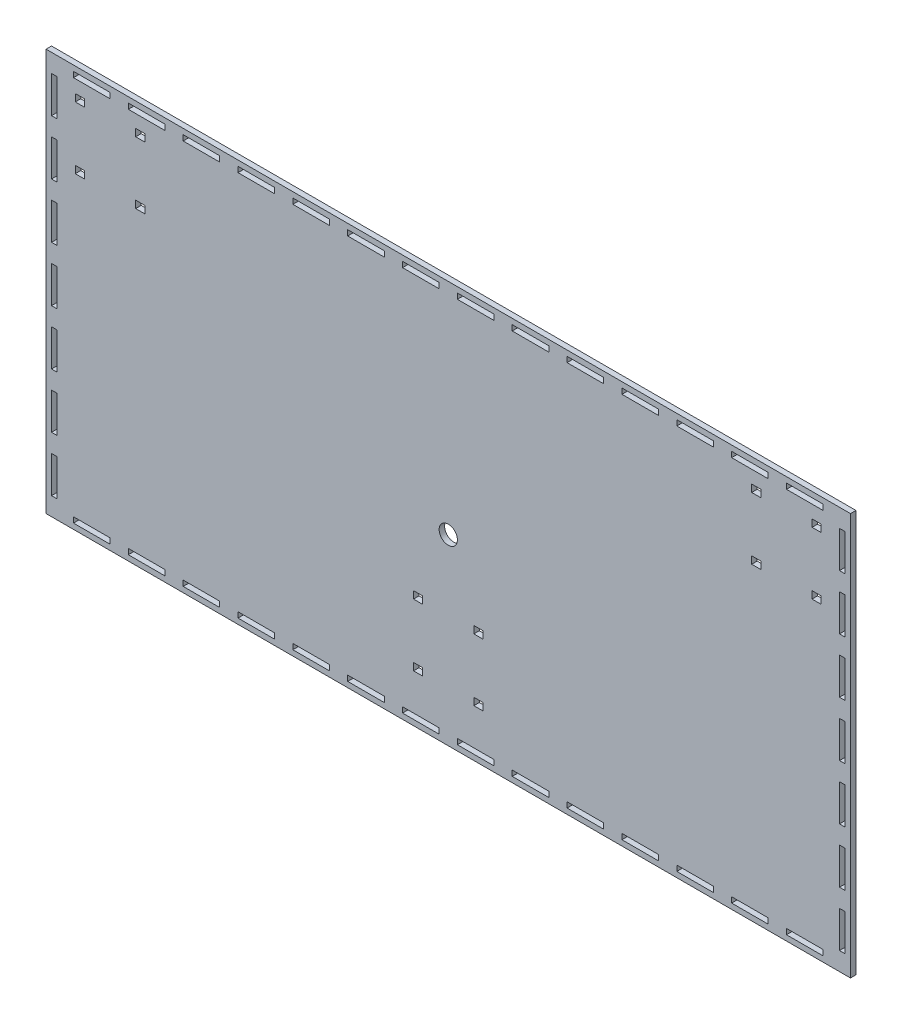
SolidWorks part; units mm, degrees
ref_plane "Plan de face" through (0, 0, 0) normal (0, 0, 1) x (1, 0, 0)
ref_plane "Plan de dessus" through (0, 0, 0) normal (0, 1, 0) x (1, 0, 0)
ref_plane "Plan de droite" through (0, 0, 0) normal (1, 0, 0) x (0, 0, -1)
sketch "Esquisse1" plane through (0, 0, 0) normal (0, 0, 1) x (1, 0, 0)
  line L1 (-220, 110) -> (220, 110)
  line L2 (-220, 110) -> (-220, -110)
  line L3 (-220, -110) -> (220, -110)
  line L4 (220, 110) -> (220, -110)
  line L5 (-220, 110) -> (220, -110) construction
  line L6 (-220, -110) -> (220, 110) construction
  point P0 (0, 0)
  dimension "D1" = 440
  dimension "D2" = 220
extrude "Boss.-Extru.1" add sketch "Esquisse1" along normal blind 3
sketch "Esquisse2" plane through (0, 0, 3) normal (0, 0, 1) x (1, 0, 0)
  line L0 (-220, -10) -> (220, -10) construction
  line L1 (-220, 110) -> (-220, -110) construction
  line L2 (220, -110) -> (220, 110) construction
  line L3 (0, 110) -> (0, -110) construction
  line L4 (220, 110) -> (-220, 110) construction
  line L5 (-220, -110) -> (220, -110) construction
  circle A0 centre (0, -10) radius 5
  dimension "D2" = 10
  dimension "D1" = 100
extrude "Enlèv. mat.-Extru.1" cut sketch "Esquisse2" against normal blind 3
sketch "Esquisse3" plane through (0, 0, 3) normal (0, 0, 1) x (1, 0, 0)
  line L0 (-185, 94) -> (-185, 62) construction
  line L1 (-201, 78) -> (-169, 78) construction
  line L2 (-220, 110) -> (-220, -110) construction
  line L3 (220, 110) -> (-220, 110) construction
  line L4 (-171, 95) -> (-199, 95) construction
  line L5 (-204, 97) -> (-199, 97)
  line L6 (-204, 97) -> (-204, 93)
  line L7 (-204, 93) -> (-199, 93)
  line L8 (-199, 97) -> (-199, 93)
  line L9 (-204, 97) -> (-199, 93) construction
  line L10 (-204, 93) -> (-199, 97) construction
  line L11 (-166, 97) -> (-171, 97)
  line L12 (-166, 97) -> (-166, 93)
  line L13 (-166, 93) -> (-171, 93)
  line L14 (-171, 97) -> (-171, 93)
  line L15 (-166, 97) -> (-171, 93) construction
  line L16 (-166, 93) -> (-171, 97) construction
  line L17 (-166, 63) -> (-171, 63)
  line L18 (-166, 59) -> (-166, 63)
  line L19 (-166, 59) -> (-171, 59)
  line L20 (-171, 59) -> (-171, 63)
  line L21 (-199, 59) -> (-199, 63)
  line L22 (-204, 63) -> (-199, 63)
  line L23 (-204, 59) -> (-204, 63)
  line L24 (-204, 59) -> (-199, 59)
  line L25 (0, 110) -> (0, -110) construction
  line L26 (-220, -110) -> (220, -110) construction
  line L27 (-220, 0) -> (220, 0) construction
  line L28 (220, -110) -> (220, 110) construction
  line L29 (171, 59) -> (171, 63)
  line L30 (166, 59) -> (171, 59)
  line L31 (166, 59) -> (166, 63)
  line L32 (166, 63) -> (171, 63)
  line L33 (204, 59) -> (199, 59)
  line L34 (204, 59) -> (204, 63)
  line L35 (204, 63) -> (199, 63)
  line L36 (199, 59) -> (199, 63)
  line L37 (166, 93) -> (171, 93)
  line L38 (166, 97) -> (166, 93)
  line L39 (166, 97) -> (171, 97)
  line L40 (171, 97) -> (171, 93)
  line L41 (199, 97) -> (199, 93)
  line L42 (204, 93) -> (199, 93)
  line L43 (204, 97) -> (204, 93)
  line L44 (204, 97) -> (199, 97)
  line L53 (-19, -50) -> (-14, -50)
  line L54 (-19, -46) -> (-19, -50)
  line L55 (-19, -46) -> (-14, -46)
  line L56 (-14, -46) -> (-14, -50)
  line L57 (14, -46) -> (14, -50)
  line L58 (19, -46) -> (14, -46)
  line L59 (19, -46) -> (19, -50)
  line L60 (19, -50) -> (14, -50)
  line L61 (-28.5071, -65) -> (30.7799, -65) construction
  line L63 (19, -84) -> (14, -84)
  line L64 (19, -84) -> (19, -80)
  line L65 (19, -80) -> (14, -80)
  line L66 (14, -84) -> (14, -80)
  line L67 (-14, -84) -> (-14, -80)
  line L68 (-19, -84) -> (-14, -84)
  line L69 (-19, -84) -> (-19, -80)
  line L70 (-19, -80) -> (-14, -80)
  circle A0 centre (-185, 78) radius 16 construction
  point P10 (-201.5, 95)
  point P15 (-168.5, 95)
  dimension "D1" = 35
  dimension "D3" = 32
  dimension "D2" = 32
  dimension "D4" = 5
  dimension "D5" = 4
  dimension "D6" = 28
  dimension "D7" = 5
  dimension "D8" = 4
  dimension "D9" = 15
  dimension "D10" = 14
  dimension "D11" = 4
  dimension "D12" = 5
  dimension "D13" = 14
  dimension "D14" = 60
  dimension "D15" = 15
extrude "Enlèv. mat.-Extru.2" cut sketch "Esquisse3" against normal blind 3
sketch "Esquisse4" plane through (0, 0, 3) normal (0, 0, 1) x (1, 0, 0)
  line L0 (220, 110) -> (-220, 110) construction
  line L1 (-205, 107) -> (-185, 107)
  line L2 (-205, 107) -> (-205, 104)
  line L3 (-205, 104) -> (-185, 104)
  line L4 (-185, 107) -> (-185, 104)
  line L5 (-220, 110) -> (-220, -110) construction
  line L6 (-175, 107) -> (-175, 104)
  line L7 (-175, 107) -> (-155, 107)
  line L8 (-155, 107) -> (-155, 104)
  line L9 (-175, 104) -> (-155, 104)
  line L10 (-145, 107) -> (-145, 104)
  line L11 (-145, 107) -> (-125, 107)
  line L12 (-125, 107) -> (-125, 104)
  line L13 (-145, 104) -> (-125, 104)
  line L14 (-115, 107) -> (-115, 104)
  line L15 (-115, 107) -> (-95, 107)
  line L16 (-95, 107) -> (-95, 104)
  line L17 (-115, 104) -> (-95, 104)
  line L18 (-85, 107) -> (-85, 104)
  line L19 (-85, 107) -> (-65, 107)
  line L20 (-65, 107) -> (-65, 104)
  line L21 (-85, 104) -> (-65, 104)
  line L22 (-55, 107) -> (-55, 104)
  line L23 (-55, 107) -> (-35, 107)
  line L24 (-35, 107) -> (-35, 104)
  line L25 (-55, 104) -> (-35, 104)
  line L26 (-25, 107) -> (-25, 104)
  line L27 (-25, 107) -> (-5, 107)
  line L28 (-5, 107) -> (-5, 104)
  line L29 (-25, 104) -> (-5, 104)
  line L30 (5, 107) -> (5, 104)
  line L31 (5, 107) -> (25, 107)
  line L32 (25, 107) -> (25, 104)
  line L33 (5, 104) -> (25, 104)
  line L34 (35, 107) -> (35, 104)
  line L35 (35, 107) -> (55, 107)
  line L36 (55, 107) -> (55, 104)
  line L37 (35, 104) -> (55, 104)
  line L38 (65, 107) -> (65, 104)
  line L39 (65, 107) -> (85, 107)
  line L40 (85, 107) -> (85, 104)
  line L41 (65, 104) -> (85, 104)
  line L126 (95, 107) -> (95, 104)
  line L127 (95, 107) -> (115, 107)
  line L128 (115, 107) -> (115, 104)
  line L129 (95, 104) -> (115, 104)
  line L130 (125, 107) -> (125, 104)
  line L131 (125, 107) -> (145, 107)
  line L132 (145, 107) -> (145, 104)
  line L133 (125, 104) -> (145, 104)
  line L134 (155, 107) -> (155, 104)
  line L135 (155, 107) -> (175, 107)
  line L136 (175, 107) -> (175, 104)
  line L137 (155, 104) -> (175, 104)
  line L138 (185, 107) -> (185, 104)
  line L139 (185, 107) -> (205, 107)
  line L140 (205, 107) -> (205, 104)
  line L141 (185, 104) -> (205, 104)
  line L143 (-252.8812, 0) -> (272.7656, 0) construction
  line L144 (-220, -110) -> (220, -110) construction
  line L145 (185, -107) -> (205, -107)
  line L146 (205, -107) -> (205, -104)
  line L147 (185, -104) -> (205, -104)
  line L148 (185, -107) -> (185, -104)
  line L149 (155, -107) -> (175, -107)
  line L150 (175, -107) -> (175, -104)
  line L151 (155, -104) -> (175, -104)
  line L152 (155, -107) -> (155, -104)
  line L153 (125, -107) -> (145, -107)
  line L154 (145, -107) -> (145, -104)
  line L155 (125, -104) -> (145, -104)
  line L156 (125, -107) -> (125, -104)
  line L157 (95, -107) -> (115, -107)
  line L158 (115, -107) -> (115, -104)
  line L159 (95, -104) -> (115, -104)
  line L160 (95, -107) -> (95, -104)
  line L161 (65, -107) -> (85, -107)
  line L162 (85, -107) -> (85, -104)
  line L163 (65, -104) -> (85, -104)
  line L164 (65, -107) -> (65, -104)
  line L165 (35, -107) -> (55, -107)
  line L166 (55, -107) -> (55, -104)
  line L167 (35, -104) -> (55, -104)
  line L168 (35, -107) -> (35, -104)
  line L169 (5, -107) -> (25, -107)
  line L170 (25, -107) -> (25, -104)
  line L171 (5, -104) -> (25, -104)
  line L172 (5, -107) -> (5, -104)
  line L173 (-25, -107) -> (-5, -107)
  line L174 (-5, -107) -> (-5, -104)
  line L175 (-25, -104) -> (-5, -104)
  line L176 (-25, -107) -> (-25, -104)
  line L177 (-55, -107) -> (-35, -107)
  line L178 (-35, -107) -> (-35, -104)
  line L179 (-55, -104) -> (-35, -104)
  line L180 (-55, -107) -> (-55, -104)
  line L181 (-85, -107) -> (-65, -107)
  line L182 (-65, -107) -> (-65, -104)
  line L183 (-85, -104) -> (-65, -104)
  line L184 (-85, -107) -> (-85, -104)
  line L185 (-115, -107) -> (-95, -107)
  line L186 (-95, -107) -> (-95, -104)
  line L187 (-115, -104) -> (-95, -104)
  line L188 (-115, -107) -> (-115, -104)
  line L189 (-145, -107) -> (-125, -107)
  line L190 (-125, -107) -> (-125, -104)
  line L191 (-145, -104) -> (-125, -104)
  line L192 (-145, -107) -> (-145, -104)
  line L193 (-175, -107) -> (-155, -107)
  line L194 (-155, -107) -> (-155, -104)
  line L195 (-175, -104) -> (-155, -104)
  line L196 (-175, -107) -> (-175, -104)
  line L197 (-205, -104) -> (-185, -104)
  line L198 (-185, -107) -> (-185, -104)
  line L199 (-205, -107) -> (-185, -107)
  line L200 (-205, -107) -> (-205, -104)
  dimension "D1" = 20
  dimension "D2" = 3
  dimension "D3" = 3
  dimension "D4" = 15
  dimension "D6" = 10
  dimension "D7" = 110
  dimension "D5" = 14
extrude "Enlèv. mat.-Extru.3" cut sketch "Esquisse4" against normal blind 3
sketch "Esquisse5" plane through (0, 0, 3) normal (0, 0, 1) x (1, 0, 0)
  line L0 (-220, -110) -> (220, -110) construction
  line L1 (-217, -100) -> (-214, -100)
  line L2 (-217, -100) -> (-217, -80)
  line L3 (-217, -80) -> (-214, -80)
  line L4 (-214, -100) -> (-214, -80)
  line L5 (-220, 110) -> (-220, -110) construction
  line L6 (-217, -50) -> (-214, -50)
  line L7 (-217, -70) -> (-217, -50)
  line L8 (-214, -70) -> (-214, -50)
  line L9 (-217, -70) -> (-214, -70)
  line L10 (-217, -20) -> (-214, -20)
  line L11 (-217, -40) -> (-217, -20)
  line L12 (-214, -40) -> (-214, -20)
  line L13 (-217, -40) -> (-214, -40)
  line L14 (-217, 10) -> (-214, 10)
  line L15 (-217, -10) -> (-217, 10)
  line L16 (-214, -10) -> (-214, 10)
  line L17 (-217, -10) -> (-214, -10)
  line L18 (-217, 40) -> (-214, 40)
  line L19 (-217, 20) -> (-217, 40)
  line L20 (-214, 20) -> (-214, 40)
  line L21 (-217, 20) -> (-214, 20)
  line L22 (-217, 70) -> (-214, 70)
  line L23 (-217, 50) -> (-217, 70)
  line L24 (-214, 50) -> (-214, 70)
  line L25 (-217, 50) -> (-214, 50)
  line L26 (-217, 100) -> (-214, 100)
  line L27 (-217, 80) -> (-217, 100)
  line L28 (-214, 80) -> (-214, 100)
  line L29 (-217, 80) -> (-214, 80)
  line L54 (0, 110) -> (0, -110) construction
  line L55 (220, 110) -> (-220, 110) construction
  line L80 (217, 80) -> (214, 80)
  line L81 (214, 80) -> (214, 100)
  line L82 (217, 80) -> (217, 100)
  line L83 (217, 100) -> (214, 100)
  line L84 (217, 50) -> (214, 50)
  line L85 (214, 50) -> (214, 70)
  line L86 (217, 50) -> (217, 70)
  line L87 (217, 70) -> (214, 70)
  line L88 (217, 20) -> (214, 20)
  line L89 (214, 20) -> (214, 40)
  line L90 (217, 20) -> (217, 40)
  line L91 (217, 40) -> (214, 40)
  line L92 (217, -10) -> (214, -10)
  line L93 (214, -10) -> (214, 10)
  line L94 (217, -10) -> (217, 10)
  line L95 (217, 10) -> (214, 10)
  line L96 (217, -40) -> (214, -40)
  line L97 (214, -40) -> (214, -20)
  line L98 (217, -40) -> (217, -20)
  line L99 (217, -20) -> (214, -20)
  line L100 (217, -70) -> (214, -70)
  line L101 (214, -70) -> (214, -50)
  line L102 (217, -70) -> (217, -50)
  line L103 (217, -50) -> (214, -50)
  line L104 (214, -100) -> (214, -80)
  line L105 (217, -80) -> (214, -80)
  line L106 (217, -100) -> (217, -80)
  line L107 (217, -100) -> (214, -100)
  dimension "D1" = 20
  dimension "D2" = 3
  dimension "D3" = 10
  dimension "D4" = 3
  dimension "D6" = 10
  dimension "D5" = 7
extrude "Enlèv. mat.-Extru.4" cut sketch "Esquisse5" against normal blind 3
